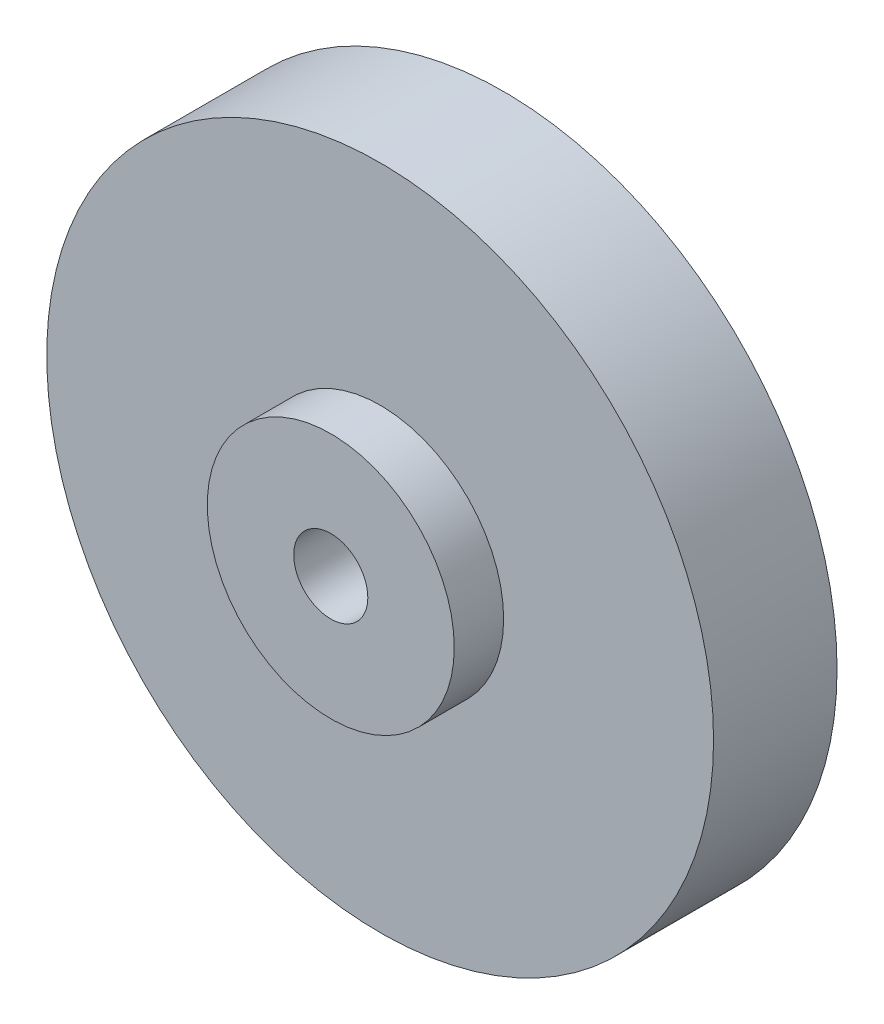
SolidWorks part; units mm, degrees
ref_plane "Front Plane" through (0, 0, 0) normal (0, 0, 1) x (1, 0, 0)
ref_plane "Top Plane" through (0, 0, 0) normal (0, 1, 0) x (1, 0, 0)
ref_plane "Right Plane" through (0, 0, 0) normal (1, 0, 0) x (0, 0, -1)
sketch "Sketch1" plane through (0, 0, 0) normal (0, 0, 1) x (1, 0, 0)
  circle A0 centre (0, 0) radius 13.5
  dimension "D1" = 27
extrude "Boss-Extrude1" add sketch "Sketch1" along normal blind 5
sketch "Sketch2" plane through (0, 0, 5) normal (0, 0, 1) x (1, 0, 0)
  circle A0 centre (0, 0) radius 5
  dimension "D1" = 10
extrude "Boss-Extrude2" add sketch "Sketch2" along normal blind 2
sketch "Sketch3" plane through (0, 0, 7) normal (0, 0, 1) x (1, 0, 0)
  circle A0 centre (0, 0) radius 1.5
extrude "Cut-Extrude1" cut sketch "Sketch3" against normal through all
chamfer "Chamfer1" distance 2 angle 45 1 edges at (1.5, 0, 0)
